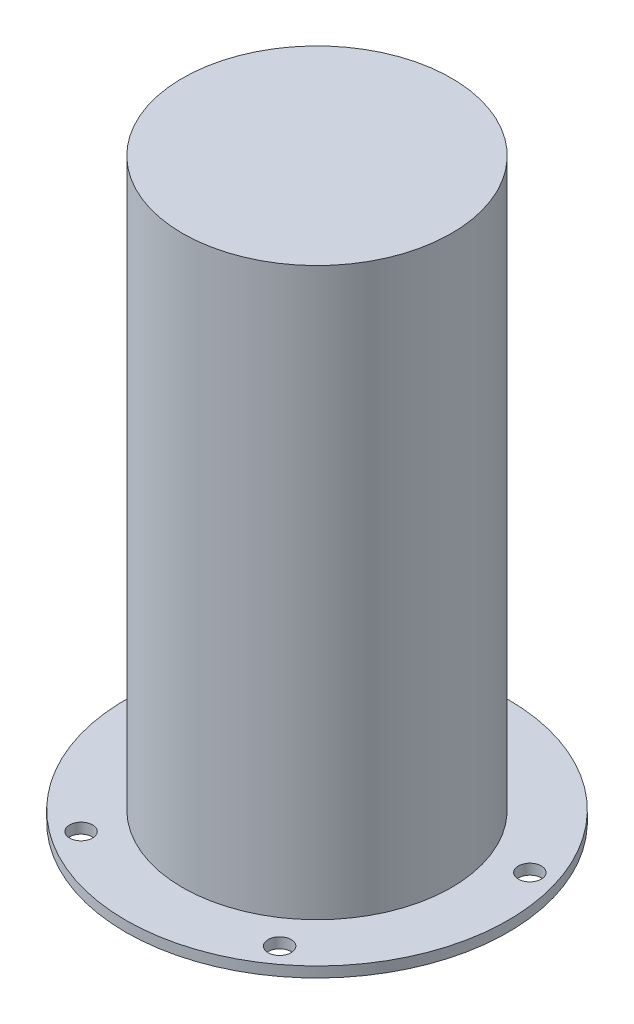
SolidWorks part; units mm, degrees
ref_plane "Front Plane" through (0, 0, 0) normal (0, 0, 1) x (1, 0, 0)
ref_plane "Top Plane" through (0, 0, 0) normal (0, 1, 0) x (1, 0, 0)
ref_plane "Right Plane" through (0, 0, 0) normal (1, 0, 0) x (0, 0, -1)
sketch "Sketch1" plane through (0, 0, 0) normal (0, 1, 0) x (1, 0, 0)
  line L0 (0, 51.9) -> (-45.2799, 51.9) construction
  line L1 (0, 55) -> (-45.2799, 55) construction
  line L2 (0, 0) -> (0, 48.6) construction
  circle A0 centre (0, 0) radius 55
  circle A1 centre (0, 0) radius 37.5
  circle A2 centre (0, 48.6) radius 3.3
  circle A3 centre (46.2213, 15.0182) radius 3.3
  circle A4 centre (28.5664, -39.3182) radius 3.3
  circle A5 centre (-28.5664, -39.3182) radius 3.3
  circle A6 centre (-46.2213, 15.0182) radius 3.3
  dimension "D1" = 110
  dimension "D2" = 75
  dimension "D3" = 6.6
  dimension "D4" = 3.1
  dimension "D6" = 48.6
  dimension "D5" = 5
extrude "Boss-Extrude1" add sketch "Sketch1" along normal blind 3
sketch "Sketch2" plane through (0, 0, 0) normal (0, 0, 1) x (1, 0, 0)
  line L0 (40.825, 1.4) -> (58.5266, 1.4) construction
  line L1 (-55, 0) -> (55, 0) construction
  line L2 (44, -1.775) -> (44, 10.0348) construction
  line L3 (0, 0) -> (0, 10.5994) construction
  circle A0 centre (40.825, -1.775) radius 3.175
  dimension "D1" = 6.35
  dimension "D2" = 1.4
  dimension "D3" = 44
revolve "Cut-Revolve1" cut sketch "Sketch2" angle 360 about L3
sketch "Sketch3" plane through (0, 3, 0) normal (0, 1, 0) x (1, 0, 0)
  circle A0 centre (0, 0) radius 38.7
  circle A1 centre (0, 0) radius 37.5
  dimension "D1" = 75
  dimension "D2" = 1.2
extrude "Boss-Extrude2" add sketch "Sketch3" along normal blind 160
sketch "Sketch4" plane through (0, 163, 0) normal (0, 1, 0) x (1, 0, 0)
  circle A0 centre (0, 0) radius 38.7 construction
  circle A1 centre (0, 0) radius 38.7
extrude "Boss-Extrude3" add sketch "Sketch4" along normal blind 3
